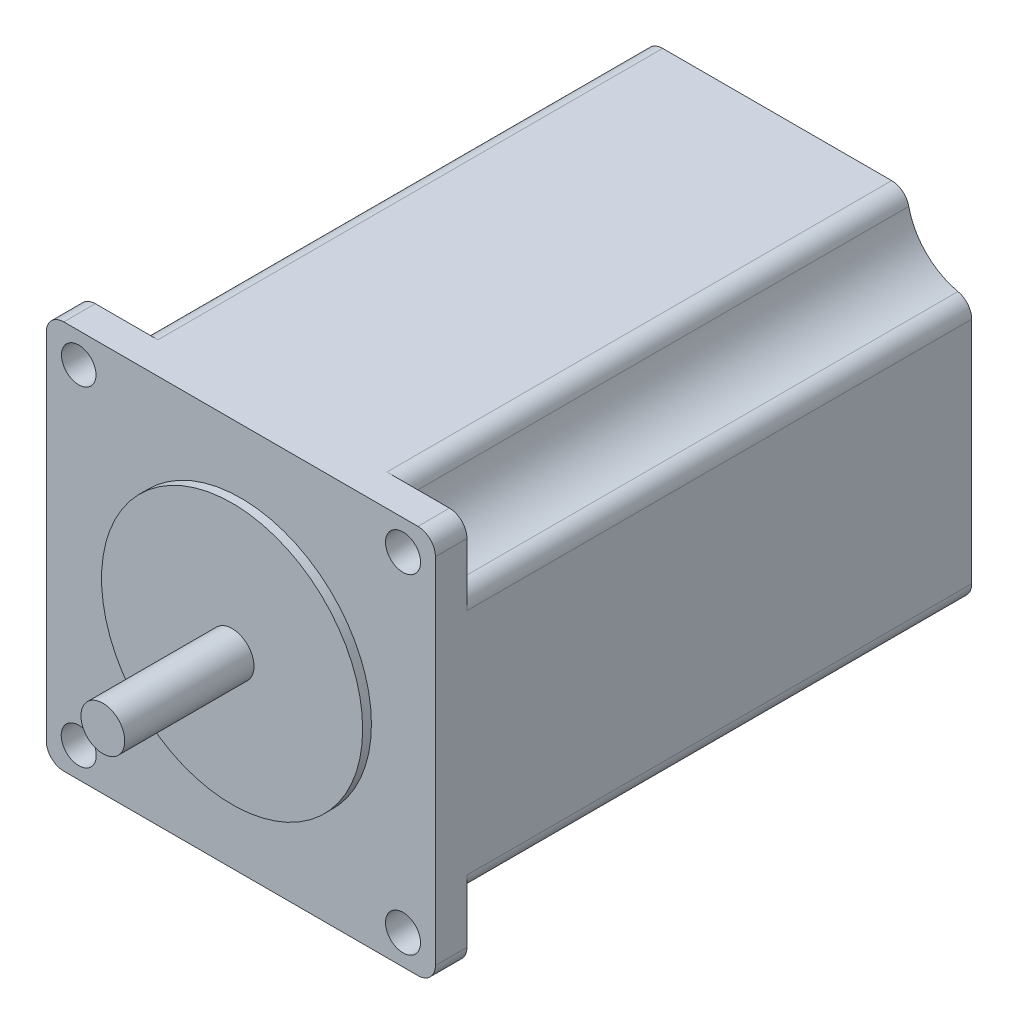
SolidWorks part; units mm, degrees
ref_plane "Front Plane" through (0, 0, 0) normal (0, 0, 1) x (1, 0, 0)
ref_plane "Top Plane" through (0, 0, 0) normal (0, 1, 0) x (1, 0, 0)
ref_plane "Right Plane" through (0, 0, 0) normal (1, 0, 0) x (0, 0, -1)
sketch "Sketch1" plane through (0, 0, 0) normal (0, 0, 1) x (1, 0, 0)
  line L1 (-25.66, 28.194) -> (25.66, 28.194)
  line L2 (-28.2, 25.654) -> (-28.2, -25.654)
  line L3 (-25.66, -28.194) -> (25.66, -28.194)
  line L4 (28.2, 25.654) -> (28.2, -25.654)
  line L5 (-28.2, 28.194) -> (28.2, -28.194) construction
  line L6 (-28.2, -28.194) -> (28.2, 28.194) construction
  arc A0 (-28.2, -25.654) -> (-25.66, -28.194) centre (-25.66, -25.654) ccw
  arc A1 (25.66, -28.194) -> (28.2, -25.654) centre (25.66, -25.654) ccw
  arc A2 (25.66, 28.194) -> (28.2, 25.654) centre (25.66, 25.654) cw
  arc A3 (-25.66, 28.194) -> (-28.2, 25.654) centre (-25.66, 25.654) ccw
  point P0 (0, 0)
  dimension "D3" = 2.54
  dimension "D1" = 56.4
  dimension "D2" = 56.388
extrude "Boss-Extrude1" add sketch "Sketch1" against normal blind 4.572
sketch "Sketch2" plane through (0, 0, 0) normal (0, 0, 1) x (1, 0, 0)
  circle A0 centre (-23.495, 23.876) radius 2.5
  circle A1 centre (23.505, 23.876) radius 2.54
  circle A2 centre (-23.495, -23.876) radius 2.54
  circle A3 centre (23.505, -23.876) radius 2.54
  dimension "D1" = 5
  dimension "D2" = 5.08
  dimension "D3" = 47
  dimension "D4" = 23.495
  dimension "D5" = 5.08
  dimension "D6" = 5.08
  dimension "D8" = 23.495
  dimension "D7" = 47
  dimension "D9" = 23.876
  dimension "D10" = 23.876
extrude "Cut-Extrude1" cut sketch "Sketch2" against normal blind 12.7
sketch "Sketch3" plane through (0, 0, 0) normal (0, 0, 1) x (1, 0, 0)
  circle A0 centre (0, 0) radius 3.175
  dimension "D1" = 6.35
extrude "Boss-Extrude2" add sketch "Sketch3" along normal blind 20
sketch "Sketch6" plane through (0, 0, -4.572) normal (0, 0, -1) x (-1, 0, 0)
  line L0 (-16.5954, 28.194) -> (16.5954, 28.194)
  line L1 (-25.66, 28.194) -> (25.66, 28.194) construction
  line L2 (-28.2, 16.5942) -> (-28.2, -16.5942)
  line L3 (-28.2, -25.654) -> (-28.2, 25.654) construction
  line L4 (-16.595, -28.194) -> (16.595, -28.194)
  line L5 (25.66, -28.194) -> (-25.66, -28.194) construction
  line L6 (28.2, 16.5936) -> (28.2, -16.5936)
  line L7 (28.2, 25.654) -> (28.2, -25.654) construction
  arc A0 (-26.203, 19.0755) -> (-19.0764, 26.1983) centre (-28.2, 28.2001) ccw
  arc A1 (-26.203, -19.0755) -> (-19.076, -26.1984) centre (-28.2, -28.2007) cw
  arc A2 (19.0762, -26.1973) -> (26.2021, -19.0751) centre (28.1941, -28.194) cw
  arc A3 (26.203, 19.0749) -> (19.0765, 26.1982) centre (28.2, 28.1994) cw
  arc A4 (16.5954, 28.194) -> (19.0765, 26.1982) centre (16.5954, 25.654) cw
  arc A5 (28.2, 16.5936) -> (26.203, 19.0749) centre (25.66, 16.5936) ccw
  arc A6 (28.2, -16.5936) -> (26.2021, -19.0751) centre (25.66, -16.5936) cw
  arc A7 (16.595, -28.194) -> (19.0762, -26.1973) centre (16.595, -25.654) ccw
  arc A8 (-16.595, -28.194) -> (-19.076, -26.1984) centre (-16.595, -25.654) cw
  arc A9 (-28.2, -16.5942) -> (-26.203, -19.0755) centre (-25.66, -16.5942) ccw
  arc A10 (-28.2, 16.5942) -> (-26.203, 19.0755) centre (-25.66, 16.5942) cw
  arc A11 (-16.5954, 28.194) -> (-19.0764, 26.1983) centre (-16.5954, 25.654) ccw
  point P16 (-28.2, 0)
  point P17 (0, 28.194)
  point P18 (28.2, 0)
  point P19 (0, -28.194)
  point P27 (18.8596, 28.194)
  point P30 (28.2, 18.8589)
  point P33 (28.2, -18.8601)
  point P36 (18.8601, -28.194)
  point P39 (-18.8589, -28.194)
  point P42 (-28.2, -18.8595)
  point P45 (-28.2, 18.8595)
  point P48 (-18.8594, 28.194)
  dimension "D5" = 2.54
  dimension "D1" = 37.719
  dimension "D2" = 37.719
  dimension "D3" = 37.719
  dimension "D4" = 37.719
extrude "Boss-Extrude3" add sketch "Sketch6" along normal blind 73.152
sketch "Sketch7" plane through (0, 0, -77.724) normal (0, 0, -1) x (-1, 0, 0)
  circle A0 centre (0, 0) radius 5.08
  dimension "D1" = 10.16
extrude "Cut-Extrude2" cut sketch "Sketch7" against normal blind 2.54
sketch "Sketch8" plane through (0, -28.194, 0) normal (0, -1, 0) x (-1, 0, 0)
  line L0 (-16.595, 77.724) -> (16.595, 77.724) construction
  line L1 (-2.2225, 73.914) -> (2.2225, 73.914)
  line L2 (-2.2225, 73.914) -> (-2.2225, 69.469)
  line L3 (-2.2225, 69.469) -> (2.2225, 69.469)
  line L4 (2.2225, 73.914) -> (2.2225, 69.469)
  line L5 (-2.2225, 73.914) -> (2.2225, 69.469) construction
  line L6 (-2.2225, 69.469) -> (2.2225, 73.914) construction
  point P0 (0, 71.6915)
  dimension "D1" = 4.445
  dimension "D2" = 4.445
  dimension "D3" = 2.2225
  dimension "D4" = 3.81
extrude "Boss-Extrude4" add sketch "Sketch8" along normal blind 2.54
sketch "Sketch9" plane through (0, 0, 0) normal (0, 0, 1) x (1, 0, 0)
  circle A0 centre (0, 0) radius 18.923
  dimension "D1" = 37.846
extrude "Boss-Extrude5" add sketch "Sketch9" along normal blind 1.27
